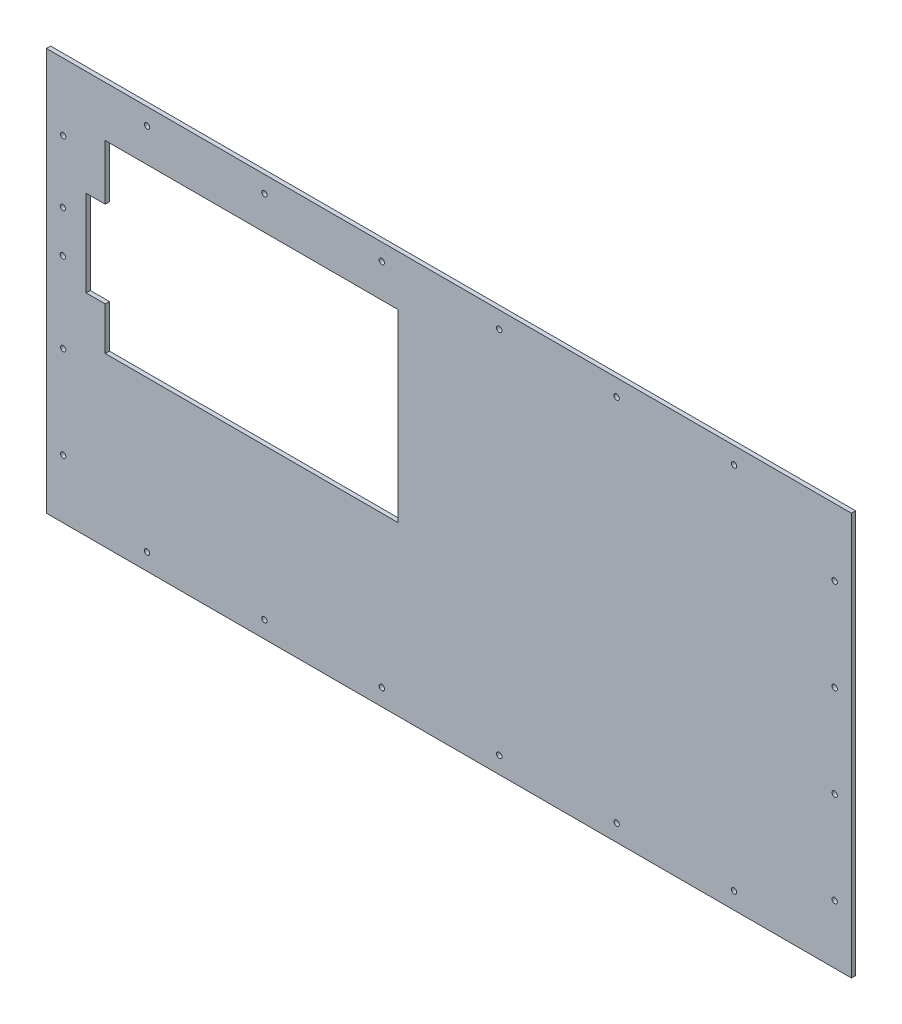
SolidWorks part; units mm, degrees
ref_plane "Front Plane" through (0, 0, 0) normal (0, 0, 1) x (1, 0, 0)
ref_plane "Top Plane" through (0, 0, 0) normal (0, 1, 0) x (1, 0, 0)
ref_plane "Right Plane" through (0, 0, 0) normal (1, 0, 0) x (0, 0, -1)
sketch "Sketch1" plane through (0, 0, 0) normal (0, 0, 1) x (1, 0, 0)
  line L1 (0, 0) -> (-609.6, 0)
  line L2 (0, 0) -> (0, 304.8)
  line L3 (0, 304.8) -> (-609.6, 304.8)
  line L4 (-609.6, 0) -> (-609.6, 304.8)
  dimension "D1" = 609.6
  dimension "D2" = 304.8
extrude "Boss-Extrude1" add sketch "Sketch1" along normal blind 3.175
sketch "Sketch5" plane through (0, 0, 3.175) normal (0, 0, 1) x (1, 0, 0)
  line L0 (-609.6, 304.8) -> (-609.6, 0) construction
  line L1 (-609.6, 0) -> (0, 0) construction
  line L2 (-609.6, 152.4) -> (0, 152.4) construction
  line L3 (0, 0) -> (0, 304.8) construction
  circle A0 centre (-533.4, 12.7) radius 2.032
  circle A1 centre (-444.5, 12.7) radius 2.032
  circle A2 centre (-355.6, 12.7) radius 2.032
  circle A3 centre (-266.7, 12.7) radius 2.032
  circle A4 centre (-177.8, 12.7) radius 2.032
  circle A5 centre (-88.9, 12.7) radius 2.032
  circle A6 centre (-88.9, 292.1) radius 2.032
  circle A7 centre (-177.8, 292.1) radius 2.032
  circle A8 centre (-266.7, 292.1) radius 2.032
  circle A9 centre (-355.6, 292.1) radius 2.032
  circle A10 centre (-444.5, 292.1) radius 2.032
  circle A11 centre (-533.4, 292.1) radius 2.032
  dimension "D1" = 4.064
  dimension "D2" = 76.2
  dimension "D5" = 88.9
  dimension "D4" = 12.7
  dimension "D3" = 6
extrude "Cut-Extrude4" cut sketch "Sketch5" against normal through all
sketch "Sketch6" plane through (0, 0, 3.175) normal (0, 0, 1) x (1, 0, 0)
  line L0 (-609.6, 304.8) -> (-609.6, 0) construction
  line L1 (0, 304.8) -> (-609.6, 304.8) construction
  line L2 (-304.8, 304.8) -> (-304.8, 0) construction
  line L3 (-609.6, 0) -> (0, 0) construction
  circle A0 centre (-596.9, 254) radius 2.032
  circle A1 centre (-596.9, 184.15) radius 2.032
  circle A2 centre (-596.9, 114.3) radius 2.032
  circle A3 centre (-596.9, 44.45) radius 2.032
  circle A4 centre (-12.7, 44.45) radius 2.032
  circle A5 centre (-12.7, 114.3) radius 2.032
  circle A6 centre (-12.7, 184.15) radius 2.032
  circle A7 centre (-12.7, 254) radius 2.032
  dimension "D1" = 4.064
  dimension "D3" = 50.8
  dimension "D5" = 69.85
  dimension "D2" = 12.7
  dimension "D4" = 4
extrude "Cut-Extrude5" cut sketch "Sketch6" against normal blind 3.175 and the other way blind 10 contours A0 | A2 | A3 | A7 | A6 | A5 | A4
sketch "Sketch20" plane through (0, 0, 3.175) normal (0, 0, 1) x (1, 0, 0)
  circle A0 centre (-597.1106, 175.0187) radius 2.032
  circle A1 centre (-597.1106, 206.7687) radius 2.032
  dimension "D1" = 4.064
  dimension "D2" = 4.064
  dimension "D3" = 31.75
extrude "Cut-Extrude17" cut sketch "Sketch20" against normal through all
sketch "Sketch8" plane through (0, 0, 3.175) normal (0, 0, 1) x (1, 0, 0)
  line L0 (0, 304.8) -> (-609.6, 304.8) construction
  line L1 (-565.0336, 266.7) -> (-343.3336, 266.7)
  line L2 (-565.0336, 266.7) -> (-565.0336, 127)
  line L3 (-565.0336, 127) -> (-343.3336, 127)
  line L4 (-343.3336, 266.7) -> (-343.3336, 127)
  line L5 (-609.6, 304.8) -> (-609.6, 0) construction
  dimension "D1" = 139.7
  dimension "D2" = 221.7
  dimension "D3" = 38.1
  dimension "D4" = 44.5664
extrude "Cut-Extrude6" cut sketch "Sketch8" against normal blind 3.175
sketch "Sketch9" plane through (0, 0, 3.175) normal (0, 0, 1) x (1, 0, 0)
  line L6 (-248.3895, 230.124) -> (-248.3895, 165.0431) construction
  line L9 (-248.3895, 165.0431) -> (-122.3895, 165.0431) construction
  line L10 (-122.3895, 165.0431) -> (-122.3895, 230.124) construction
  line L11 (-240.373, 234.95) -> (-130.373, 234.95)
  line L12 (-240.373, 234.95) -> (-240.373, 160.2171)
  line L13 (-240.373, 160.2171) -> (-130.373, 160.2171)
  line L14 (-130.373, 234.95) -> (-130.373, 160.2171)
  line L15 (-122.3895, 230.124) -> (-248.3895, 230.124) construction
  line L16 (-185.373, 234.95) -> (-185.373, 160.2171) construction
  line L17 (0, 0) -> (0, 304.8) construction
  line L18 (0, 304.8) -> (-609.6, 304.8) construction
  circle A0 centre (-248.3895, 230.124) radius 2
  circle A1 centre (-122.3895, 230.124) radius 2
  circle A2 centre (-248.3895, 165.0431) radius 2
  circle A3 centre (-122.3895, 165.0431) radius 2
  dimension "D6" = 4
  dimension "D7" = 4
  dimension "D2" = 4
  dimension "D3" = 4
  dimension "D1" = 63.0165
  dimension "D4" = 110
  dimension "D5" = 126
  dimension "D8" = 74.7329
  dimension "D9" = 122.3895
  dimension "D10" = 69.85
  dimension "D11" = 4.826
  dimension "D12" = 4.826
extrude "Cut-Extrude7" [suppressed] cut sketch "Sketch9" against normal blind 3.175
sketch "Sketch12" plane through (0, 0, 3.175) normal (0, 0, 1) x (1, 0, 0)
  line L1 (-280.5423, 249.6541) -> (-86.5423, 249.6541)
  line L2 (-280.5423, 249.6541) -> (-280.5423, 139.6541)
  line L3 (-280.5423, 139.6541) -> (-86.5423, 139.6541)
  line L4 (-86.5423, 249.6541) -> (-86.5423, 139.6541)
  dimension "D1" = 194
  dimension "D2" = 110
sketch "Sketch19" plane through (0, 0, 0) normal (0, 0, -1) x (-1, 0, 0)
  line L0 (565.0336, 266.7) -> (565.0336, 127) construction
  line L1 (565.0336, 159.5193) -> (579.5233, 159.5193)
  line L2 (565.0336, 159.5193) -> (565.0336, 224.8933)
  line L3 (565.0336, 224.8933) -> (579.5233, 224.8933)
  line L4 (579.5233, 159.5193) -> (579.5233, 224.8933)
  dimension "D1" = 65.374
  dimension "D2" = 14.4897
extrude "Cut-Extrude16" cut sketch "Sketch19" against normal through all
equation "\"D2@Sketch8\"=266.70mm-45mm"
